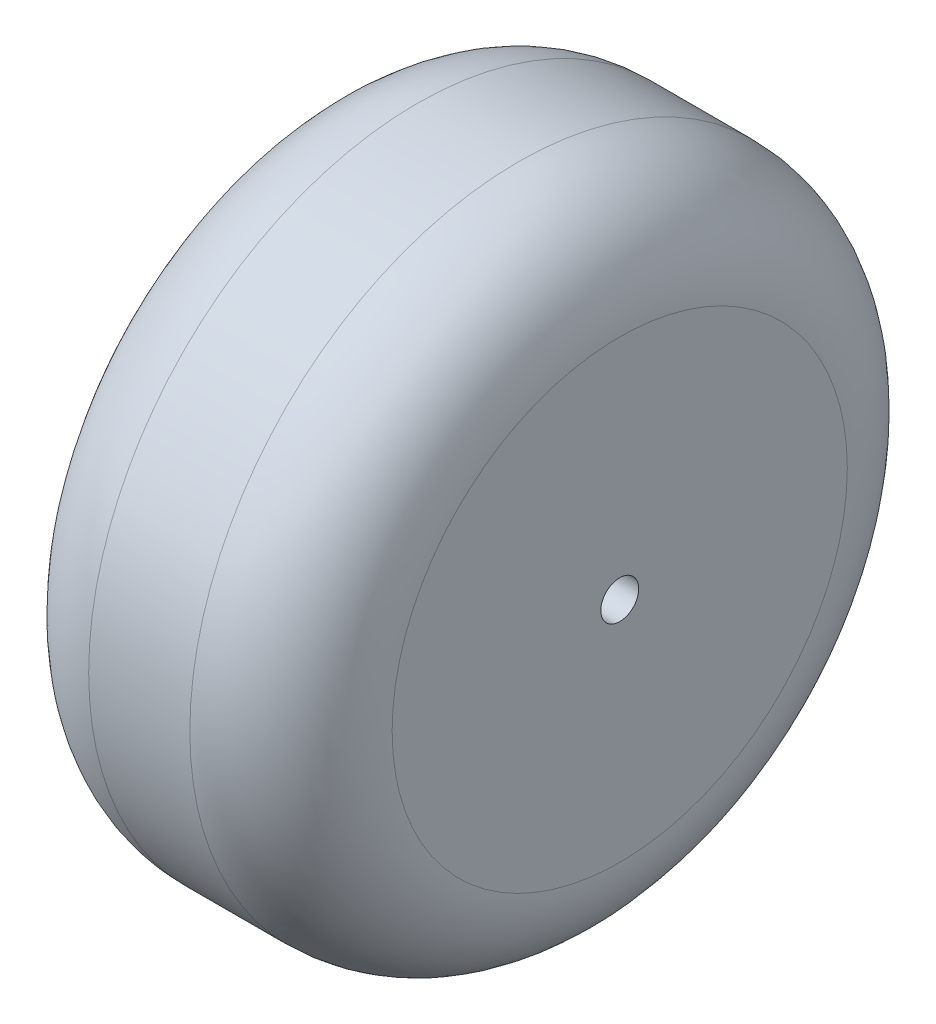
SolidWorks part; units mm, degrees
ref_plane "Front Plane" through (0, 0, 0) normal (0, 0, 1) x (1, 0, 0)
ref_plane "Top Plane" through (0, 0, 0) normal (0, 1, 0) x (1, 0, 0)
ref_plane "Right Plane" through (0, 0, 0) normal (1, 0, 0) x (0, 0, -1)
sketch "Sketch1" plane through (0, 0, 0) normal (1, 0, 0) x (0, 0, -1)
  circle A0 centre (0, 0) radius 41.275
  dimension "D1" = 82.55
extrude "Boss-Extrude1" add sketch "Sketch1" along normal blind 38.1
sketch "Sketch2" plane through (38.1, 0, 0) normal (1, 0, 0) x (0, 0, -1)
  circle A0 centre (0, 0) radius 2.3812
  dimension "D1" = 4.7625
extrude "Cut-Extrude1" cut sketch "Sketch2" against normal through all
fillet "Fillet1" radius 12.7 2 edges at (0, 0, -41.275) (38.1, 0, -41.275)
